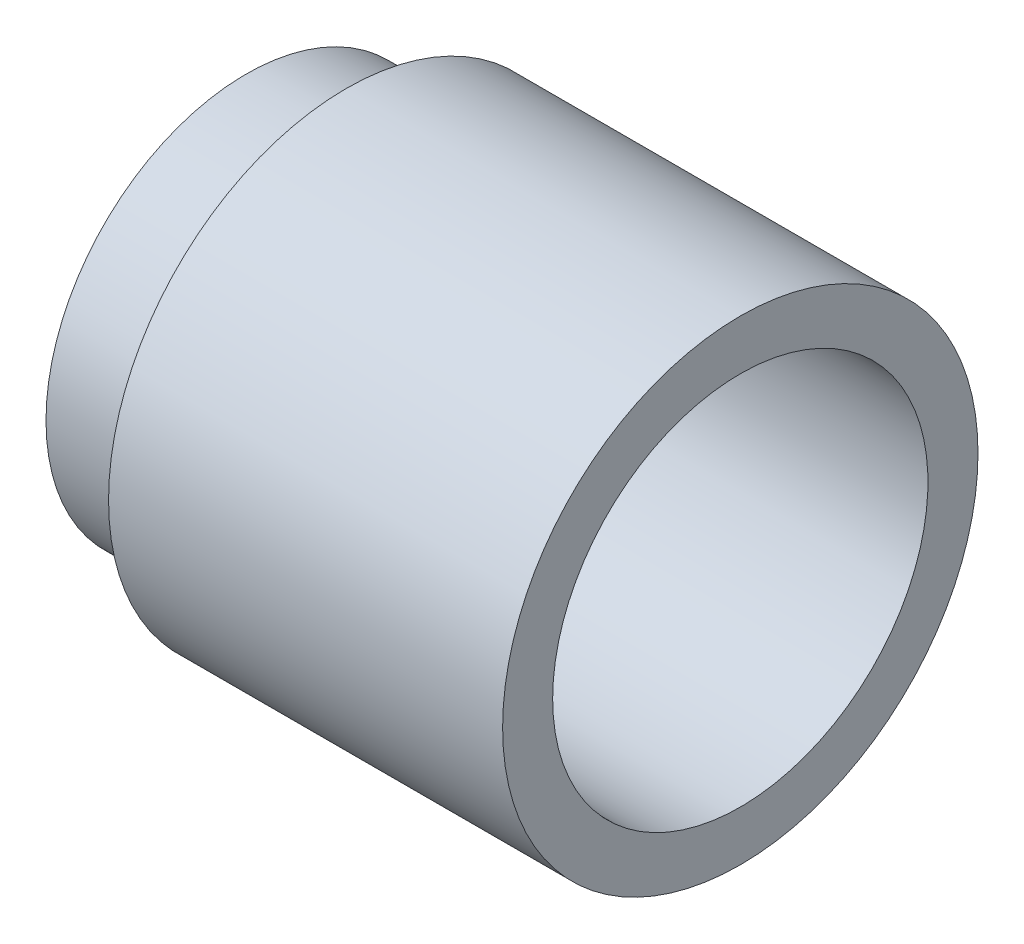
SolidWorks part; units mm, degrees
ref_plane "Plan de face" through (0, 0, 0) normal (0, 0, 1) x (1, 0, 0)
ref_plane "Plan de dessus" through (0, 0, 0) normal (0, 1, 0) x (1, 0, 0)
ref_plane "Plan de droite" through (0, 0, 0) normal (1, 0, 0) x (0, 0, -1)
sketch "Esquisse1" plane through (0, 0, 0) normal (0, 0, 1) x (1, 0, 0)
  line L0 (0, 0) -> (14.8634, 0) construction
  line L1 (0, 0) -> (0, 8) construction
  line L2 (0, 8) -> (0, 7.5)
  line L3 (0, 7.5) -> (19.75, 7.5)
  line L4 (19.75, 7.5) -> (19.75, 9.5)
  line L5 (19.75, 9.5) -> (4, 9.5)
  line L6 (4, 9.5) -> (4, 8)
  line L7 (4, 8) -> (0, 8)
  dimension "D1" = 8
  dimension "D2" = 0.5
  dimension "D3" = 4
  dimension "D4" = 15.75
  dimension "D5" = 9.5
revolve "Révolution1" add sketch "Esquisse1" angle 360 about L0
